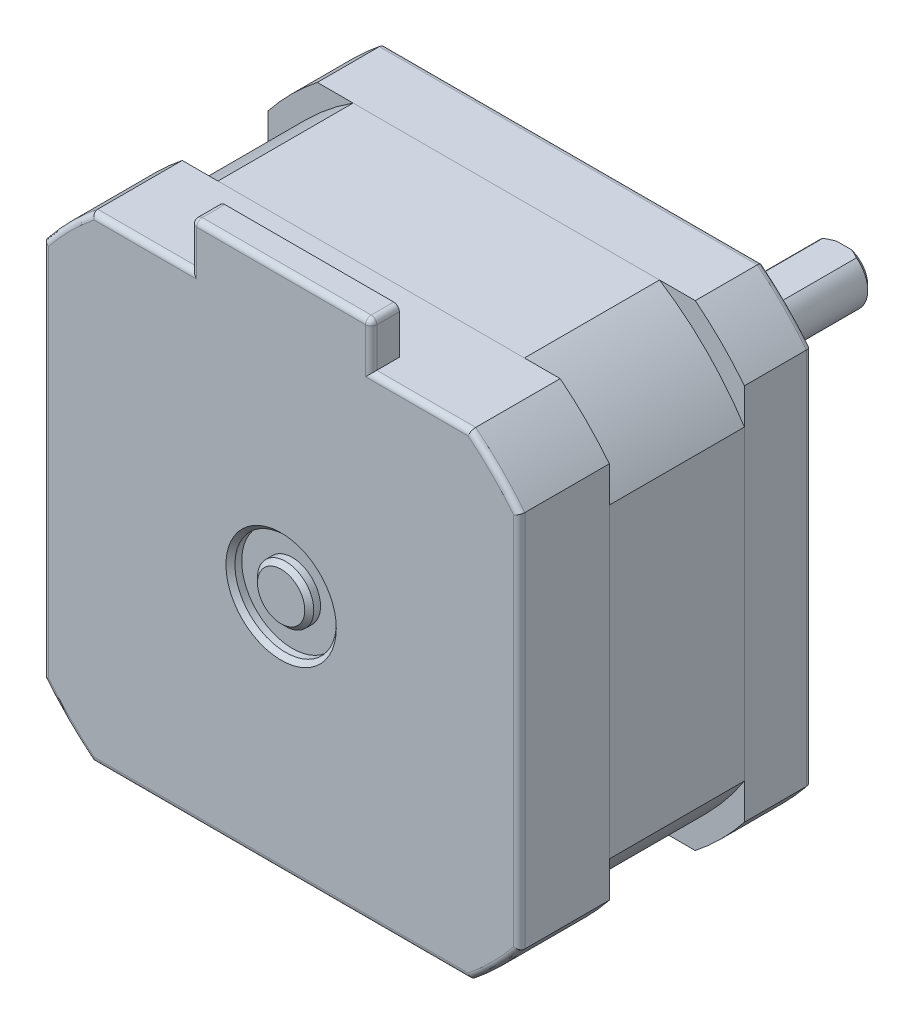
SolidWorks part; units mm, degrees
ref_plane "Plan de face" through (0, 0, 0) normal (0, 0, 1) x (1, 0, 0)
ref_plane "Plan de dessus" through (0, 0, 0) normal (0, 1, 0) x (1, 0, 0)
ref_plane "Plan de droite" through (0, 0, 0) normal (1, 0, 0) x (0, 0, -1)
sketch "Esquisse1" plane through (0, 0, 0) normal (0, 0, 1) x (1, 0, 0)
  line L0 (21.15, 16.7833) -> (21.15, -16.7833)
  line L1 (-21.15, 21.15) -> (21.15, 21.15) construction
  line L2 (-21.15, 21.15) -> (-21.15, -21.15) construction
  line L3 (-21.15, -21.15) -> (21.15, -21.15) construction
  line L4 (21.15, 21.15) -> (21.15, -21.15) construction
  line L5 (-21.15, 21.15) -> (21.15, -21.15) construction
  line L6 (-21.15, -21.15) -> (21.15, 21.15) construction
  line L7 (16.7833, -21.15) -> (-16.7833, -21.15)
  line L8 (-21.15, -16.7833) -> (-21.15, 16.7833)
  line L9 (-16.7833, 21.15) -> (16.7833, 21.15)
  arc A0 (-16.7833, 21.15) -> (-21.15, 16.7833) centre (0, 0) ccw
  arc A1 (21.15, 16.7833) -> (16.7833, 21.15) centre (0, 0) ccw
  arc A2 (-21.15, -16.7833) -> (-16.7833, -21.15) centre (0, 0) ccw
  arc A3 (16.7833, -21.15) -> (21.15, -16.7833) centre (0, 0) ccw
  point P0 (0, 0)
  dimension "D2" = 54
  dimension "D1" = 42.3
extrude "Boss.-Extru.1" add sketch "Esquisse1" along normal blind 6
sketch "Esquisse2" plane through (0, 0, 6) normal (0, 0, 1) x (1, 0, 0)
  line L23 (-13.6088, 21.15) -> (13.6088, 21.15)
  line L24 (16.7833, 21.15) -> (-16.7833, 21.15) construction
  line L25 (21.15, 13.6088) -> (21.15, -13.6088)
  line L26 (21.15, -16.7833) -> (21.15, 16.7833) construction
  line L27 (13.6088, -21.15) -> (-13.6088, -21.15)
  line L28 (-16.7833, -21.15) -> (16.7833, -21.15) construction
  line L29 (-21.15, -13.6088) -> (-21.15, 13.6088)
  line L30 (-21.15, 16.7833) -> (-21.15, -16.7833) construction
  arc A60 (-13.6088, 21.15) -> (-21.15, 13.6088) centre (0, 0) ccw
  arc A61 (21.15, 16.7833) -> (16.7833, 21.15) centre (0, 0) ccw construction
  arc A62 (21.15, 13.6088) -> (13.6088, 21.15) centre (0, 0) ccw
  arc A63 (13.6088, -21.15) -> (21.15, -13.6088) centre (0, 0) ccw
  arc A64 (-21.15, -13.6088) -> (-13.6088, -21.15) centre (0, 0) ccw
  dimension "D1" = 1.85
extrude "Boss.-Extru.2" add sketch "Esquisse2" along normal blind 12 separate body
sketch "Esquisse3" plane through (0, 0, 18) normal (0, 0, 1) x (1, 0, 0)
  line L0 (-16.7833, -21.15) -> (16.7833, -21.15) construction
  line L1 (21.15, -16.7833) -> (21.15, 16.7833) construction
  line L2 (16.7833, 21.15) -> (-16.7833, 21.15) construction
  line L3 (-21.15, 16.7833) -> (-21.15, -16.7833) construction
  line L4 (-16.7833, -21.15) -> (16.7833, -21.15)
  line L5 (21.15, -16.7833) -> (21.15, 16.7833)
  line L6 (16.7833, 21.15) -> (-16.7833, 21.15)
  line L7 (-21.15, 16.7833) -> (-21.15, -16.7833)
  arc A0 (-21.15, -16.7833) -> (-16.7833, -21.15) centre (0, 0) ccw construction
  arc A1 (16.7833, -21.15) -> (21.15, -16.7833) centre (0, 0) ccw construction
  arc A2 (21.15, 16.7833) -> (16.7833, 21.15) centre (0, 0) ccw construction
  arc A3 (-16.7833, 21.15) -> (-21.15, 16.7833) centre (0, 0) ccw construction
  arc A4 (-21.15, -16.7833) -> (-16.7833, -21.15) centre (0, 0) ccw
  arc A5 (16.7833, -21.15) -> (21.15, -16.7833) centre (0, 0) ccw
  arc A6 (21.15, 16.7833) -> (16.7833, 21.15) centre (0, 0) ccw
  arc A7 (-16.7833, 21.15) -> (-21.15, 16.7833) centre (0, 0) ccw
extrude "Boss.-Extru.3" add sketch "Esquisse3" along normal blind 8 separate body
sketch "Esquisse4" plane through (0, 21.15, 0) normal (0, 1, 0) x (1, 0, 0)
  line L0 (16.7833, -26) -> (-16.7833, -26) construction
  line L1 (8, -26) -> (-8, -26)
  line L2 (8, -26) -> (8, -23.5)
  line L3 (8, -23.5) -> (-8, -23.5)
  line L4 (-8, -26) -> (-8, -23.5)
  line L5 (0, 0) -> (0, -23.5) construction
  dimension "D1" = 2.5
  dimension "D2" = 16
extrude "Boss.-Extru.4" add sketch "Esquisse4" along normal blind 4
sketch "Esquisse5" plane through (0, 0, 0) normal (1, 0, 0) x (0, 0, -1)
  line L0 (0, 0) -> (-78.698, 0) construction
  line L2 (2, 11) -> (0, 11)
  line L3 (2, 11) -> (2, 4.5)
  line L4 (2, 4.5) -> (0, 4.5)
  line L5 (0, 11) -> (0, 4.5)
  line L6 (0, -16.7833) -> (0, 16.7833) construction
  line L7 (24, 0) -> (0, 0)
  line L8 (24, 0) -> (24, 2.5)
  line L9 (24, 2.5) -> (0, 2.5)
  line L10 (0, 0) -> (0, 2.5)
  dimension "D1" = 2
  dimension "D2" = 22
  dimension "D3" = 9
  dimension "D4" = 5
  dimension "D5" = 24
revolve "Révolution1" add sketch "Esquisse5" angle 360 about L0
fillet "Congé1" radius 0.5 14 edges at (-21.15, 0, 26) (-19.0919, 19.0919, 26) (-12.3916, 21.15, 26) (-8, 23.15, 26) (0, 25.15, 26) (8, 23.15, 26) (12.3916, 21.15, 26) (19.0919, 19.0919, 26) (21.15, 0, 26) (19.0919, -19.0919, 26) (0, -21.15, 26) (-19.0919, -19.0919, 26) (-8, 25.15, 24.75) (8, 25.15, 24.75)
fillet "Congé2" radius 0.5 8 edges at (-19.0919, 19.0919, 0) (-21.15, 0, 0) (-19.0919, -19.0919, 0) (0, -21.15, 0) (19.0919, -19.0919, 0) (21.15, 0, 0) (0, 21.15, 0) (19.0919, 19.0919, 0)
chamfer "Chanfrein1" distance 0.4 angle 45 1 edges at (-2.5, 0, -24)
chamfer "Chanfrein2" distance 0.4 angle 45 1 edges at (-4.5, 0, -2)
sketch "Esquisse6" plane through (0, 0, 0) normal (1, 0, 0) x (0, 0, -1)
  line L0 (0, -2.5) -> (23.6, -2.5) construction
  line L1 (24, 2.5) -> (9, 2.5)
  line L2 (24, 2.5) -> (24, 2)
  line L3 (24, 2) -> (9, 2)
  line L4 (9, 2.5) -> (9, 2)
  line L5 (24, -2.1) -> (24, 2.1) construction
  line L6 (23.6, 2.5) -> (0, 2.5) construction
  dimension "D1" = 4.5
  dimension "D2" = 15
extrude "Enlèv. mat.-Extru.1" cut sketch "Esquisse6" against normal through all both and the other way through all
sketch "Esquisse7" plane through (0, 0, 26) normal (0, 0, 1) x (1, 0, 0)
  circle A0 centre (0, 0) radius 2.5
  circle A1 centre (0, 0) radius 4.5
  dimension "D1" = 5
  dimension "D2" = 9
extrude "Enlèv. mat.-Extru.2" cut sketch "Esquisse7" against normal blind 1
chamfer "Chanfrein3" distance 0.4 angle 45 2 edges at (4.5, 0, 26) (2.5, 0, 26)
hole_wizard "Trou taraudé M31" positions "Esquisse8" profile "Esquisse9" tap size "M3" standard "ISO"
sketch "Esquisse8" plane through (0, 0, 0) normal (0, 0, -1) x (-1, 0, 0)
  line L0 (-15.5, 15.5) -> (15.5, 15.5) construction
  line L1 (15.5, 15.5) -> (15.5, -15.5) construction
  line L2 (15.5, -15.5) -> (-15.5, -15.5) construction
  line L3 (-15.5, -15.5) -> (-15.5, 15.5) construction
  circle A0 centre (0, 0) radius 21.9203 construction
  point P5 (-15.5, 15.5)
  point P6 (15.5, 15.5)
  point P7 (15.5, -15.5)
  point P8 (-15.5, -15.5)
  dimension "D1" = 31
sketch "Esquisse9" plane through (15.5, -15.5, 0) normal (1, 0, 0) x (0, 1, 0)
  line L0 (0, 0) -> (0, 5.7511)
  line L1 (0, 5.7511) -> (1.25, 5)
  line L2 (1.25, 5) -> (1.25, 0)
  line L5 (1.25, 0) -> (0, 0)
  line L10 (0, 5.7511) -> (-1.25, 5) construction
  line L11 (0, -6.35) -> (0, 107.95) construction
  dimension "Diamètre du trou pour taraudage" = 2.5
  dimension "Profondeur du trou pour taraudage" = 5
  dimension "Angle de pointe" = 118
cosmetic thread "Filetage de perçage1" parameters "D1"=5, "D2"=3
cosmetic thread "Filetage de perçage2" parameters "D1"=5, "D2"=3
cosmetic thread "Filetage de perçage3" parameters "D1"=5, "D2"=3
cosmetic thread "Filetage de perçage4" parameters "D1"=5, "D2"=3
